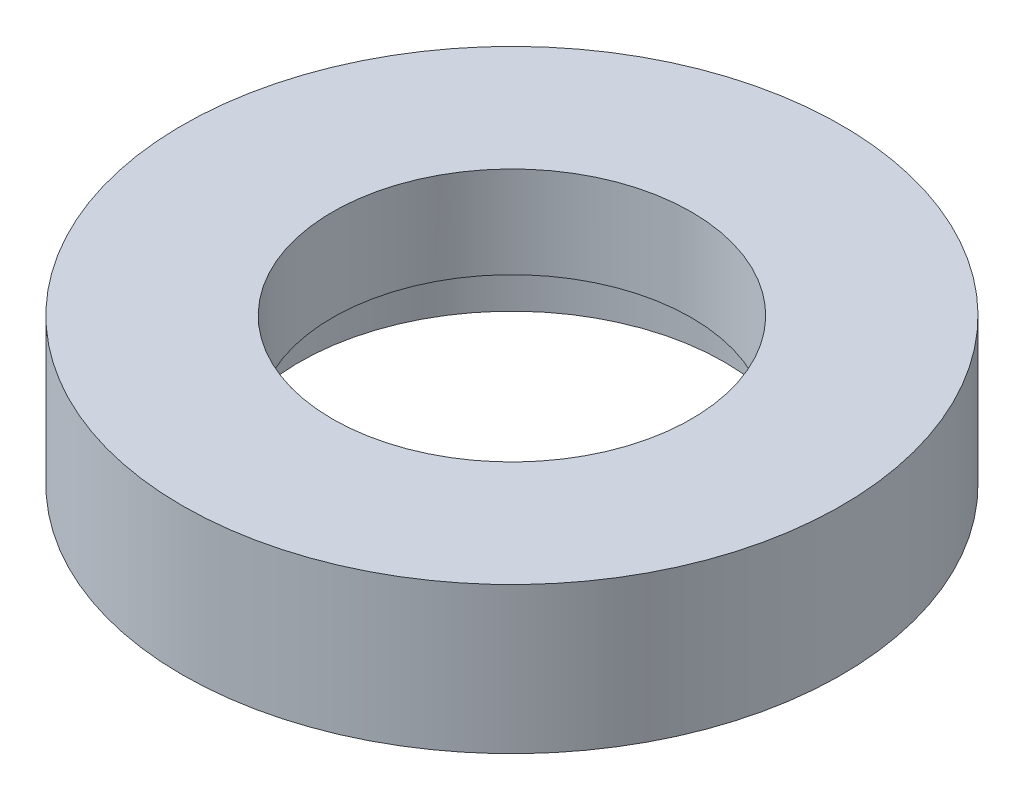
SolidWorks part; units mm, degrees
ref_plane "Front Plane" through (0, 0, 0) normal (0, 0, 1) x (1, 0, 0)
ref_plane "Top Plane" through (0, 0, 0) normal (0, 1, 0) x (1, 0, 0)
ref_plane "Right Plane" through (0, 0, 0) normal (1, 0, 0) x (0, 0, -1)
sketch "Sketch1" plane through (0, 0, 0) normal (0, 1, 0) x (1, 0, 0)
  circle A0 centre (0, 0) radius 4.5
  circle A1 centre (0, 0) radius 2.45
  dimension "D1" = 9
  dimension "D2" = 4.9
extrude "Boss-Extrude1" add sketch "Sketch1" along normal blind 2
sketch "Sketch2" plane through (0, 0, 0) normal (0, -1, 0) x (-1, 0, 0)
  circle A0 centre (0, 0) radius 2.9
  circle A1 centre (0, 0) radius 4.5 construction
  dimension "D1" = 5.8
extrude "Cut-Extrude1" cut sketch "Sketch2" against normal blind 0.75
